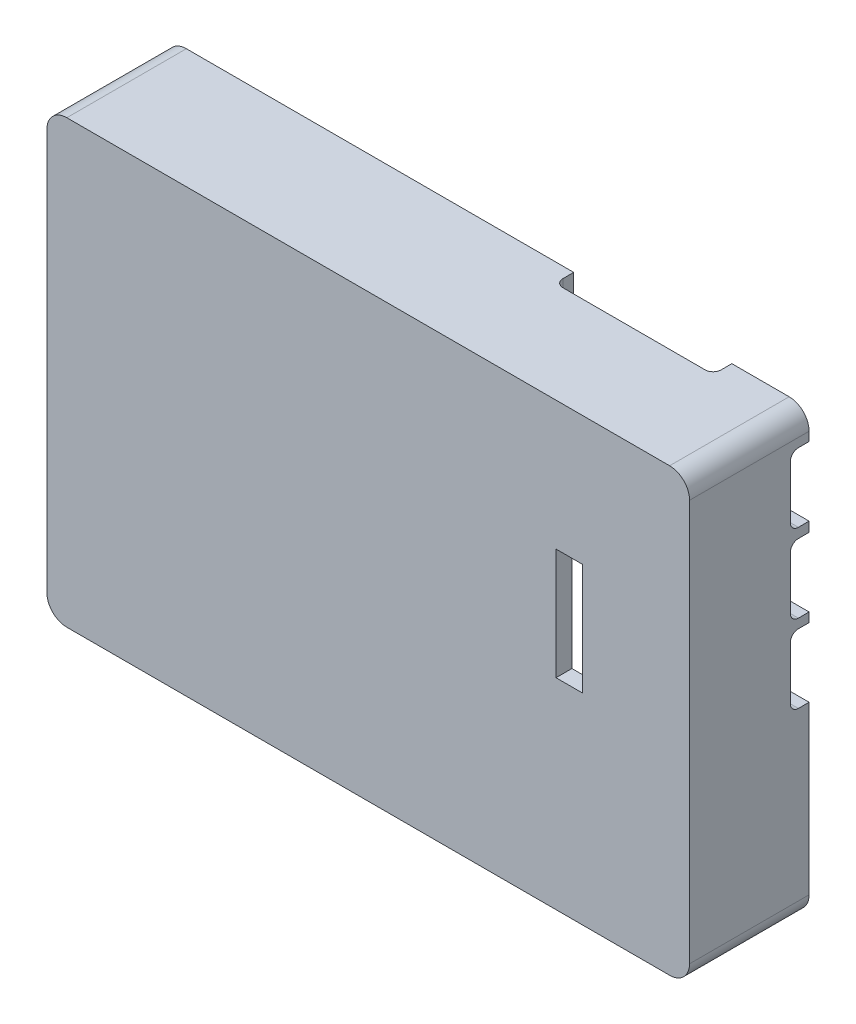
SolidWorks part; units mm, degrees
ref_plane "前视基准面" through (0, 0, 0) normal (0, 0, 1) x (1, 0, 0)
ref_plane "上视基准面" through (0, 0, 0) normal (0, 1, 0) x (1, 0, 0)
ref_plane "右视基准面" through (0, 0, 0) normal (1, 0, 0) x (0, 0, -1)
sketch "草图1" plane through (0, 0, 0) normal (0, 0, 1) x (1, 0, 0)
  line L0 (-46.7234, -29.7816) -> (27.9274, -29.7816) construction
  line L1 (-46.7234, -5.0927) -> (-46.7234, -54.4704) construction
  line L2 (27.9274, -44.5935) -> (27.9274, -5.0927) construction
  circle A0 centre (-25.174, -5.08) radius 2.5
  circle A2 centre (-25.174, -54.4831) radius 2.5
  circle A3 centre (27.9401, -46.1934) radius 2.5
extrude "凸台-拉伸1" add sketch "草图1" along normal blind 2.5
sketch "草图2" plane through (0, 0, 0) normal (0, 0, -1) x (-1, 0, 0)
  circle A0 centre (25.174, -5.08) radius 1.5
  circle A1 centre (25.174, -54.4831) radius 1.5
  circle A2 centre (-27.9401, -46.1934) radius 1.5
  dimension "D1" = 3
extrude "凸台-拉伸2" add sketch "草图2" along normal blind 2.5
sketch "草图3" plane through (0, 0, 0) normal (0, 0, -1) x (-1, 0, 0)
  line L1 (-8.0015, -26.6968) -> (-2.9409, -26.6968)
  line L2 (-8.0015, -26.6968) -> (-8.0015, -13.083)
  line L3 (-8.0015, -13.083) -> (-2.9409, -13.083)
  line L4 (-2.9409, -26.6968) -> (-2.9409, -13.083)
  line L5 (-8.0015, -26.6968) -> (-2.9409, -13.083) construction
  line L6 (-8.0015, -13.083) -> (-2.9409, -26.6968) construction
  point P0 (-5.4712, -19.8899)
extrude "凸台-拉伸3" add sketch "草图3" against normal blind 2.5 separate body
sketch "草图4" plane through (0, 0, 2.5) normal (0, 0, 1) x (1, 0, 0)
  line L1 (-49.7234, -2.0927) -> (30.9274, -2.0927)
  line L2 (-49.7234, -2.0927) -> (-49.7234, -57.4704)
  line L3 (-49.7234, -57.4704) -> (30.9274, -57.4704)
  line L4 (30.9274, -2.0927) -> (30.9274, -57.4704)
extrude "凸台-拉伸4" add sketch "草图4" along normal blind 2
sketch "草图5" plane through (0, 0, 2.5) normal (0, 0, -1) x (-1, 0, 0)
  line L0 (47.2234, -54.9704) -> (47.2234, -4.5927)
  line L1 (47.2234, -4.5927) -> (-28.4274, -4.5927)
  line L2 (-28.4274, -4.5927) -> (-28.4274, -54.9704)
  line L3 (-28.4274, -54.9704) -> (47.2234, -54.9704)
  line L4 (49.7234, -57.4704) -> (49.7234, -2.0927)
  line L5 (49.7234, -2.0927) -> (-30.9274, -2.0927)
  line L6 (-30.9274, -2.0927) -> (-30.9274, -57.4704)
  line L7 (-30.9274, -57.4704) -> (49.7234, -57.4704)
  line L8 (49.7234, -57.4704) -> (49.7234, -2.0927)
  line L9 (49.7234, -2.0927) -> (-30.9274, -2.0927)
  line L10 (-30.9274, -2.0927) -> (-30.9274, -57.4704)
  line L11 (-30.9274, -57.4704) -> (49.7234, -57.4704)
  dimension "D1" = 0
  dimension "D2" = 2.5
extrude "凸台-拉伸5" add sketch "草图5" along normal blind 13
fillet "圆角1" radius 2.5 4 edges at (30.9274, -2.0927, -3) (-49.7234, -2.0927, -3) (-49.7234, -57.4704, -3) (30.9274, -57.4704, -3)
sketch "草图7" plane through (0, -57.4704, 0) normal (0, -1, 0) x (1, 0, 0)
  line L0 (-1.6754, -3.0801) -> (-6.1754, -3.0801) construction
  line L1 (-1.6754, -6.5801) -> (-6.1754, -6.5801)
  line L2 (-1.6754, 0.4199) -> (-6.1754, 0.4199)
  arc A0 (-1.6754, -6.5801) -> (-1.6754, 0.4199) centre (-1.6754, -3.0801) ccw
  arc A1 (-6.1754, 0.4199) -> (-6.1754, -6.5801) centre (-6.1754, -3.0801) ccw
  point P2 (-3.9254, -3.0801)
  point P7 (1.8246, -3.0801)
  point P8 (-9.6754, -3.0801)
  dimension "D1" = 7
  dimension "D2" = 11.5
extrude "切除-拉伸1" cut sketch "草图7" against normal blind 2.6
sketch "草图8" plane through (0, 0, 4.5) normal (0, 0, 1) x (1, 0, 0)
  line L1 (14.1655, -18.2753) -> (17.4809, -18.2753)
  line L2 (14.1655, -18.2753) -> (14.1655, -32.2619)
  line L3 (14.1655, -32.2619) -> (17.4809, -32.2619)
  line L4 (17.4809, -18.2753) -> (17.4809, -32.2619)
extrude "切除-拉伸2" cut sketch "草图8" against normal blind 2
sketch "草图9" plane through (30.9274, 0, 0) normal (1, 0, 0) x (0, 0, -1)
  line L0 (10.5, -4.5927) -> (10.5, -54.9704) construction
  line L1 (8.15, -5.7086) -> (10.5, -5.7086)
  line L2 (8.15, -5.7086) -> (8.15, -14.3586)
  line L3 (8.15, -14.3586) -> (10.5, -14.3586)
  line L4 (10.5, -5.7086) -> (10.5, -14.3586)
  line L5 (5.8001, -24.0326) -> (2.2501, -24.0326) construction
  line L6 (8.15, -15.5826) -> (10.5, -15.5826)
  line L7 (8.15, -15.5826) -> (8.15, -24.2305)
  line L8 (8.15, -24.2305) -> (10.5, -24.2305)
  line L9 (10.5, -15.5826) -> (10.5, -24.2305)
  line L10 (5.8001, -15.7826) -> (2.2501, -15.7826) construction
  line L11 (5.8001, -14.1586) -> (2.2501, -14.1586) construction
  line L12 (5.8001, -5.9086) -> (2.2501, -5.9086) construction
  line L13 (5.8001, -25.5931) -> (2.2501, -25.5931) construction
  line L14 (10.5, -25.3931) -> (8.15, -25.3931)
  line L15 (10.5, -25.3931) -> (10.5, -34.0431)
  line L16 (10.5, -34.0431) -> (8.15, -34.0431)
  line L17 (8.15, -25.3931) -> (8.15, -34.0431)
  line L18 (5.8001, -33.8431) -> (2.2501, -33.8431) construction
  dimension "D1" = 0.198
  dimension "D2" = 0.2
  dimension "D3" = 0.2
  dimension "D4" = 0.2
  dimension "D5" = 0.2
  dimension "D6" = 0.2
  dimension "D7" = 2.35
extrude "切除-拉伸3" cut sketch "草图9" against normal blind 3
fillet "圆角2" radius 1 6 edges at (29.6774, -34.0431, -8.15) (29.6774, -25.3931, -8.15) (29.6774, -24.2305, -8.15) (29.6774, -15.5826, -8.15) (29.6774, -14.3586, -8.15) (29.6774, -5.7086, -8.15)
sketch "草图10" plane through (0, -2.0927, 0) normal (0, 1, 0) x (1, 0, 0)
  line L0 (-47.2234, 10.5) -> (28.4274, 10.5) construction
  line L1 (21.2346, 8.15) -> (1.3901, 8.15)
  line L2 (21.2346, 8.15) -> (21.2346, 10.5)
  line L3 (21.2346, 10.5) -> (1.3901, 10.5)
  line L4 (1.3901, 8.15) -> (1.3901, 10.5)
  line L5 (1.5901, 5.8001) -> (1.5901, 2.2501) construction
  dimension "D1" = 0.2
extrude "切除-拉伸4" cut sketch "草图10" against normal blind 3
fillet "圆角3" radius 1 2 edges at (1.3901, -3.3427, -8.15) (21.2346, -3.3427, -8.15)
sketch "草图11" plane through (0, -57.4704, 0) normal (0, -1, 0) x (1, 0, 0)
  circle A0 centre (-18.5303, -6.9132) radius 1.25
  dimension "D1" = 2.5
extrude "切除-拉伸5" cut sketch "草图11" against normal blind 6.8
